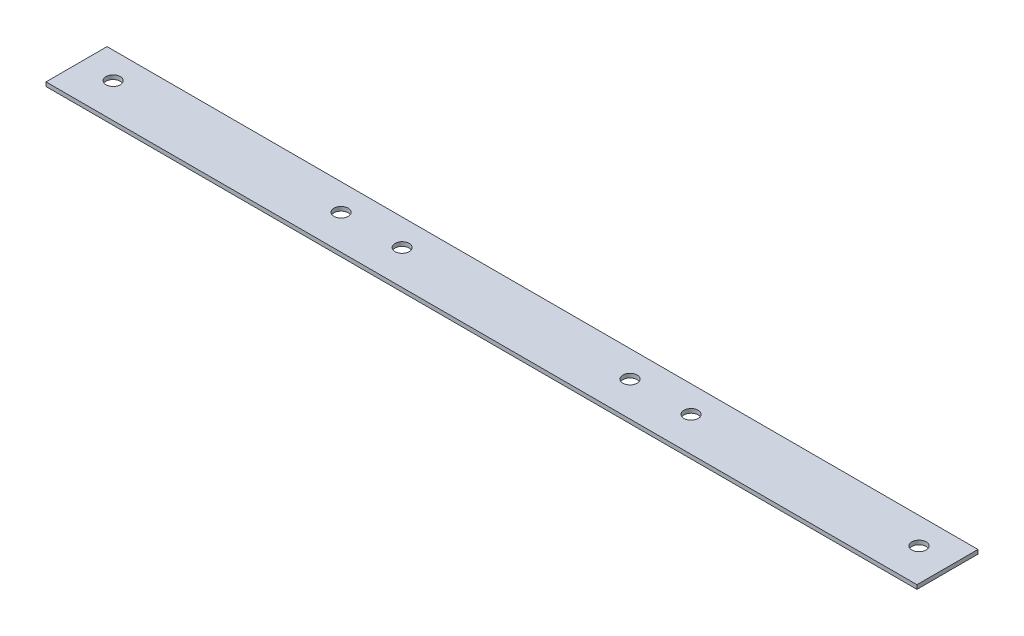
SolidWorks part; units mm, degrees
material "Простая углеродистая сталь"
ref_plane "Спереди" through (0, 0, 0) normal (0, 0, 1) x (1, 0, 0)
ref_plane "Сверху" through (0, 0, 0) normal (0, 1, 0) x (1, 0, 0)
ref_plane "Справа" through (0, 0, 0) normal (1, 0, 0) x (0, 0, -1)
sketch "Эскиз1" plane through (0, 0, 0) normal (0, 1, 0) x (1, 0, 0)
  line L1 (0, 0) -> (214, 0)
  line L2 (0, 0) -> (0, 15)
  line L3 (0, 15) -> (214, 15)
  line L4 (214, 0) -> (214, 15)
  circle A2 centre (64, 8.5) radius 1.75
  circle A3 centre (8, 8.5) radius 1.75
  circle A4 centre (79, 8.5) radius 1.75
  circle A5 centre (135, 8.5) radius 1.75
  circle A6 centre (150, 8.5) radius 1.75
  circle A7 centre (206, 8.5) radius 1.75
  dimension "D1" = 3
extrude "Бобышка-Вытянуть1" add sketch "Эскиз1" along normal blind 1 contours L2 L1 L4 L3
